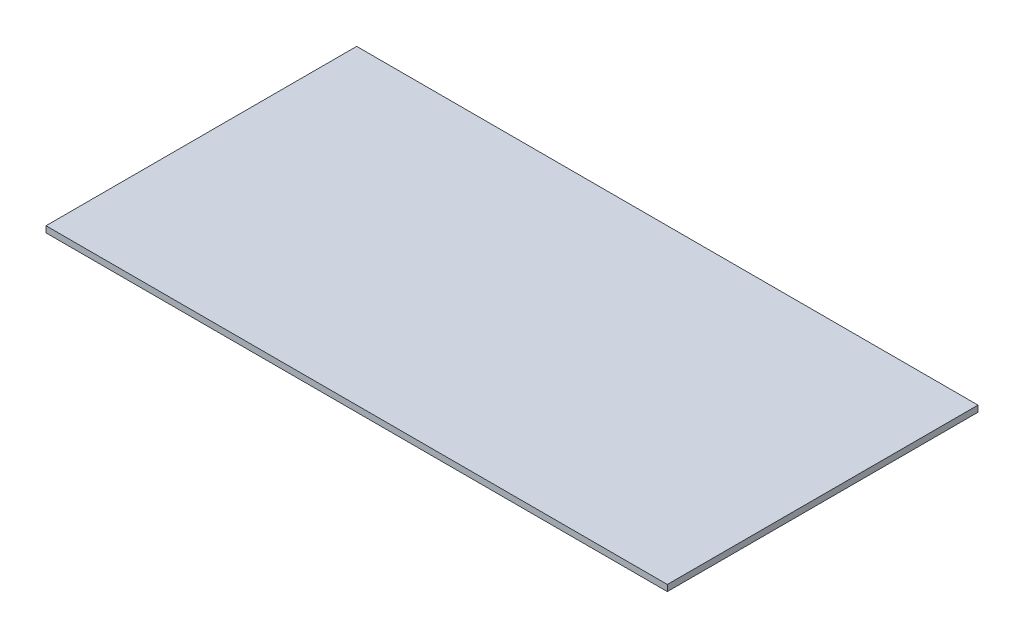
SolidWorks part; units mm, degrees
material "Ductile Iron"
ref_plane "Front Plane" through (0, 0, 0) normal (0, 0, 1) x (1, 0, 0)
ref_plane "Top Plane" through (0, 0, 0) normal (0, 1, 0) x (1, 0, 0)
ref_plane "Right Plane" through (0, 0, 0) normal (1, 0, 0) x (0, 0, -1)
sketch "Sketch1" plane through (0, 0, 0) normal (0, 1, 0) x (1, 0, 0)
  line L1 (-500, 250) -> (500, 250)
  line L2 (-500, 250) -> (-500, -250)
  line L3 (-500, -250) -> (500, -250)
  line L4 (500, 250) -> (500, -250)
  line L5 (-500, 250) -> (500, -250) construction
  line L6 (-500, -250) -> (500, 250) construction
  point P0 (0, 0)
  dimension "D1" = 500
  dimension "D2" = 1000
extrude "Boss-Extrude1" add sketch "Sketch1" along normal blind 10
ref_point "centerofground"
